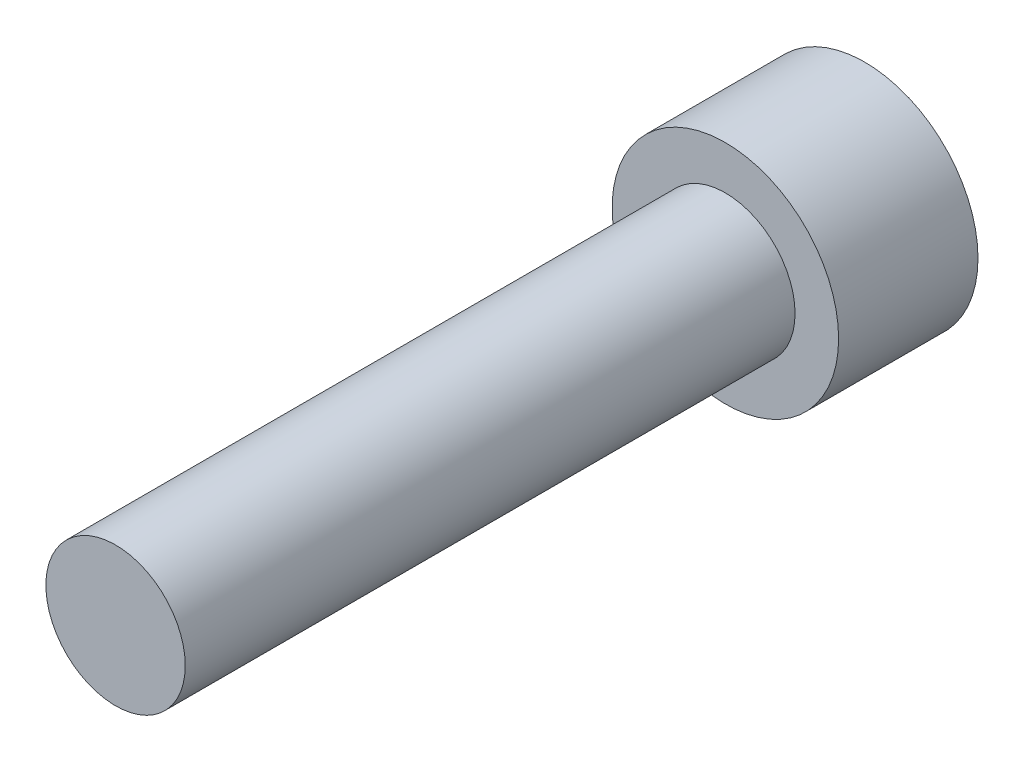
SolidWorks part; units mm, degrees
ref_plane "前视基准面" through (0, 0, 0) normal (0, 0, 1) x (1, 0, 0)
ref_plane "上视基准面" through (0, 0, 0) normal (0, 1, 0) x (1, 0, 0)
ref_plane "右视基准面" through (0, 0, 0) normal (1, 0, 0) x (0, 0, -1)
sketch "草图1" plane through (0, 0, 0) normal (0, 0, 1) x (1, 0, 0)
  circle A0 centre (-10.1589, 10.2421) radius 6.5
  dimension "D1" = 13
extrude "凸台-拉伸1" add sketch "草图1" along normal blind 8
ref_point "点1"
sketch "草图2" plane through (0, 0, 8) normal (0, 0, 1) x (1, 0, 0)
  circle A0 centre (-10.1589, 10.2421) radius 4
  dimension "D1" = 8
extrude "凸台-拉伸2" add sketch "草图2" along normal blind 35
